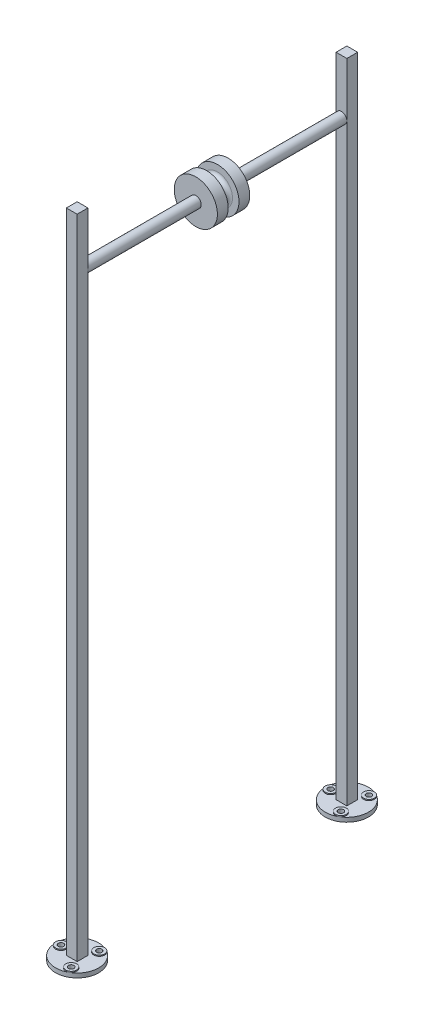
SolidWorks part; units mm, degrees
ref_plane "Front Plane" through (0, 0, 0) normal (0, 0, 1) x (1, 0, 0)
ref_plane "Top Plane" through (0, 0, 0) normal (0, 1, 0) x (1, 0, 0)
ref_plane "Right Plane" through (0, 0, 0) normal (1, 0, 0) x (0, 0, -1)
sketch "Sketch1" plane through (0, 0, 0) normal (0, 1, 0) x (1, 0, 0)
  line L0 (0, -317.5) -> (0, 317.5) construction
  line L1 (-209.0663, 0) -> (188.7838, 0) construction
  circle A0 centre (0, 317.5) radius 50.8
  circle A2 centre (-38.1, 317.5) radius 6.35
  circle A3 centre (19.05, 350.4956) radius 6.35
  circle A4 centre (19.05, 284.5044) radius 6.35
  circle A5 centre (0, -317.5) radius 50.8
  circle A6 centre (19.05, -284.5044) radius 6.35
  circle A7 centre (19.05, -350.4956) radius 6.35
  circle A8 centre (-38.1, -317.5) radius 6.35
  point P6 (0, 0)
  dimension "D2" = 101.6
  dimension "D6" = 12.7
  dimension "D7" = 12.7
  dimension "D8" = 12.7
  dimension "D1" = 635
extrude "Boss-Extrude1" add sketch "Sketch1" along normal blind 10.16
sketch "Sketch2" plane through (0, 10.16, 0) normal (0, 1, 0) x (1, 0, 0)
  line L0 (0, -317.5) -> (0, 317.5) construction
  line L1 (-157.447, 0) -> (161.5632, 0) construction
  line L3 (-12.7, 330.2) -> (12.7, 330.2)
  line L4 (-12.7, 330.2) -> (-12.7, 304.8)
  line L5 (-12.7, 304.8) -> (12.7, 304.8)
  line L6 (12.7, 330.2) -> (12.7, 304.8)
  line L7 (-12.7, 330.2) -> (12.7, 304.8) construction
  line L8 (-12.7, 304.8) -> (12.7, 330.2) construction
  line L9 (-12.7, -304.8) -> (12.7, -304.8)
  line L10 (-12.7, -304.8) -> (-12.7, -330.2)
  line L11 (-12.7, -330.2) -> (12.7, -330.2)
  line L12 (12.7, -304.8) -> (12.7, -330.2)
  line L13 (-12.7, -304.8) -> (12.7, -330.2) construction
  line L14 (-12.7, -330.2) -> (12.7, -304.8) construction
  point P7 (0, 0)
  dimension "D1" = 25.4
  dimension "D2" = 25.4
  dimension "D3" = 25.4
  dimension "D4" = 25.4
extrude "Boss-Extrude2" add sketch "Sketch2" along normal blind 1524
sketch "Sketch3" plane through (0, 0, 304.8) normal (0, 0, -1) x (-1, 0, 0)
  line L0 (-12.7, 1534.16) -> (12.7, 1534.16) construction
  circle A0 centre (0, 1407.16) radius 12.7
  dimension "D1" = 25.4
  dimension "D2" = 127
sketch "Sketch4" plane through (0, 0, -304.8) normal (0, 0, 1) x (1, 0, 0)
  line L0 (-12.7, 1534.16) -> (12.7, 1534.16) construction
  circle A0 centre (0, 1407.16) radius 12.7
  dimension "D1" = 25.4
  dimension "D2" = 127
sketch "Sketch5" plane through (0, 0, 0) normal (1, 0, 0) x (0, 0, -1)
  line L0 (-304.8, 1407.16) -> (304.8, 1407.16)
sweep "Sweep1" add profiles "Sketch3" path "Sketch5"
sketch "Sketch7" plane through (0, 0, 0) normal (1, 0, 0) x (0, 0, -1)
  line L0 (-304.8, 1407.16) -> (304.8, 1407.16) construction
  line L1 (0, 1506.0303) -> (0, 1307.7239) construction
  line L2 (-38.1, 1419.86) -> (-38.1, 1457.96)
  line L3 (304.8, 1419.86) -> (-304.8, 1419.86) construction
  line L4 (-38.1, 1457.96) -> (-12.7, 1457.96)
  line L5 (-12.7, 1457.96) -> (-12.7, 1442.72)
  line L6 (-2.54, 1432.56) -> (2.54, 1432.56)
  line L7 (12.7, 1457.96) -> (12.7, 1442.72)
  line L8 (38.1, 1457.96) -> (12.7, 1457.96)
  line L9 (38.1, 1419.86) -> (38.1, 1457.96)
  line L10 (-38.1, 1419.86) -> (38.1, 1419.86)
  arc A0 (-12.7, 1442.72) -> (-2.54, 1432.56) centre (-2.54, 1442.72) ccw
  arc A1 (12.7, 1442.72) -> (2.54, 1432.56) centre (2.54, 1442.72) cw
  point P16 (-12.7, 1432.56)
  point P18 (0, 1432.56)
  dimension "D5" = 10.16
  dimension "D1" = 25.4
  dimension "D2" = 38.1
  dimension "D3" = 12.7
  dimension "D4" = 25.4
revolve "Revolve2" add sketch "Sketch7" angle 360 about L0
sketch "Sketch8" plane through (0, 10.16, 0) normal (0, 1, 0) x (1, 0, 0)
  circle A0 centre (-38.1, -317.5) radius 6.35
  circle A1 centre (-38.1, -317.5) radius 12.7
  circle A2 centre (19.05, -284.5044) radius 6.35
  circle A3 centre (19.05, -284.5044) radius 12.7
  circle A4 centre (19.05, -350.4956) radius 12.7
  circle A5 centre (19.05, -350.4956) radius 6.35
  circle A6 centre (19.05, 350.4956) radius 6.35
  circle A7 centre (19.05, 350.4956) radius 12.7
  circle A8 centre (19.05, 284.5044) radius 6.35
  circle A9 centre (19.05, 284.5044) radius 12.7
  circle A10 centre (-38.1, 317.5) radius 6.35
  circle A11 centre (-38.1, 317.5) radius 12.7
  dimension "D1" = 25.4
  dimension "D2" = 25.4
  dimension "D3" = 25.4
  dimension "D4" = 25.4
  dimension "D5" = 25.4
  dimension "D6" = 25.4
extrude "Boss-Extrude3" add sketch "Sketch8" along normal blind 2.54
